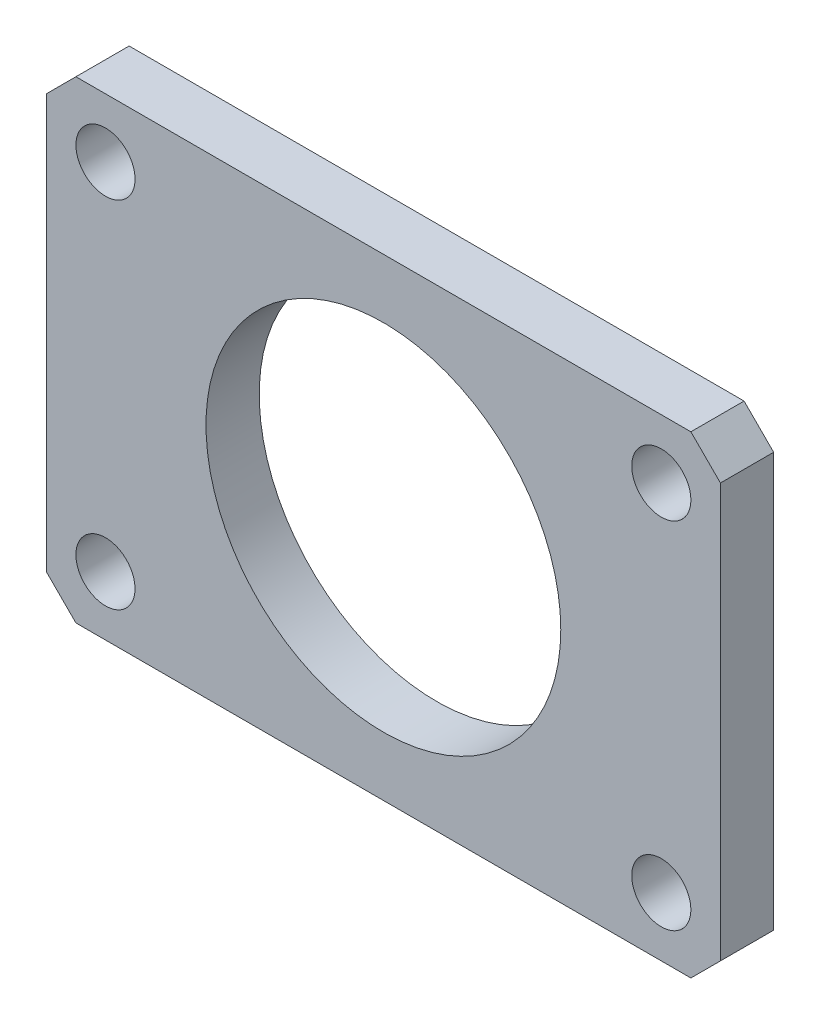
SolidWorks part; units mm, degrees
material "Сталь"
ref_plane "Спереди" through (0, 0, 0) normal (0, 0, 1) x (1, 0, 0)
ref_plane "Сверху" through (0, 0, 0) normal (0, 1, 0) x (1, 0, 0)
ref_plane "Справа" through (0, 0, 0) normal (1, 0, 0) x (0, 0, -1)
sketch "Эскиз1" plane through (0, 0, 0) normal (0, 0, 1) x (1, 0, 0)
  line L1 (-14.25, -10) -> (14.25, -10)
  line L2 (-14.25, -10) -> (-14.25, 10)
  line L3 (-14.25, 10) -> (14.25, 10)
  line L4 (14.25, -10) -> (14.25, 10)
  line L5 (-14.25, -10) -> (14.25, 10) construction
  line L6 (-14.25, 10) -> (14.25, -10) construction
  circle A0 centre (9.25, 5) radius 2.5
  point P0 (0, 0)
  dimension "D3" = 5
  dimension "D4" = 5
  dimension "D5" = 5
  dimension "D1" = 28.5
  dimension "D2" = 20
extrude "Бобышка-Вытянуть1" add sketch "Эскиз1" along normal blind 4.5
chamfer "Фаска1" distance 2.5 angle 45 1 edges at (14.25, 10, 2.25)
mirror "Зеркальное отражение1" about plane through (-14.25, -10, 4.5) normal (0, 1, 0) of bodies 105
mirror "Зеркальное отражение2" about plane through (-14.25, -10, 4.5) normal (1, 0, 0) of bodies 106
sketch "Эскиз2" plane through (0, 0, 4.5) normal (0, 0, 1) x (1, 0, 0)
  line L0 (-42.75, -10) -> (14.25, -10) construction
  line L1 (-42.75, -27.5) -> (-42.75, 7.5) construction
  line L2 (14.25, -27.5) -> (14.25, 7.5) construction
  circle A0 centre (-14.25, -10) radius 15
  dimension "D1" = 30
extrude "Вырез-Вытянуть1" cut sketch "Эскиз2" against normal through all
